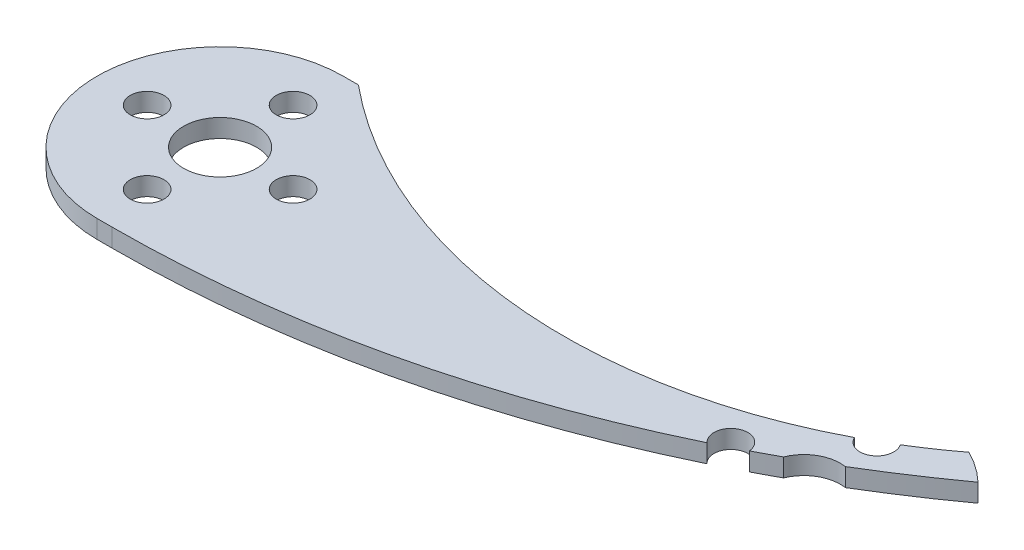
SolidWorks part; units mm, degrees
ref_plane "Front Plane" through (0, 0, 0) normal (0, 0, 1) x (1, 0, 0)
ref_plane "Top Plane" through (0, 0, 0) normal (0, 1, 0) x (1, 0, 0)
ref_plane "Right Plane" through (0, 0, 0) normal (1, 0, 0) x (0, 0, -1)
sketch "Sketch1" plane through (0, 0, 0) normal (0, 1, 0) x (1, 0, 0)
  line L0 (39.2725, 22.9769) -> (-24.7275, 22.9769)
  line L1 (-24.7275, -4.0231) -> (39.2725, -4.0231)
  arc A0 (-24.7275, 22.9769) -> (-24.7275, -4.0231) centre (-24.7275, 9.4769) ccw
  arc A1 (39.2725, -4.0231) -> (39.2725, 22.9769) centre (39.2725, 9.4769) ccw
  circle A2 centre (-24.7275, 17.4769) radius 1.85
  circle A3 centre (-24.7275, 9.4769) radius 4
  circle A4 centre (-32.7275, 9.4769) radius 1.85
  circle A5 centre (-24.7275, 1.4769) radius 1.85
  circle A6 centre (-16.7275, 9.4769) radius 1.85
  circle A7 centre (39.2725, 17.4769) radius 1.85
  circle A8 centre (39.2725, 9.4769) radius 4
  circle A9 centre (31.2725, 9.4769) radius 1.85
  circle A10 centre (47.2725, 9.4769) radius 1.85
  circle A11 centre (39.2725, 1.4769) radius 1.85
extrude "Boss-Extrude1" add sketch "Sketch1" along normal blind 2
sketch "Sketch2" plane through (0, 2, 0) normal (0, 1, 0) x (1, 0, 0)
  line L0 (39.2725, 22.9769) -> (-24.7275, 22.9769) construction
  line L1 (-24.7275, -4.0231) -> (39.2725, -4.0231) construction
  line L2 (-23.0675, 22.9769) -> (42.7774, 34.8887)
  line L3 (42.7774, 34.8887) -> (45.2781, 21.5676)
  line L4 (48.6162, 19.2209) -> (77.2151, 13.3996)
  line L5 (77.2151, 13.3996) -> (46.3589, -30.1297)
  line L6 (46.3589, -30.1297) -> (-23.0675, -4.0231)
  arc A0 (-23.0675, 22.9769) -> (45.2781, 21.5676) centre (11.9959, 65.4601) ccw
  arc A1 (39.2725, -4.0231) -> (39.2725, 22.9769) centre (39.2725, 9.4769) ccw construction
  arc A2 (-23.0675, -4.0231) -> (48.6162, 19.2209) centre (-23.0675, 118.134) ccw
extrude "Cut-Extrude1" cut sketch "Sketch2" against normal through all
